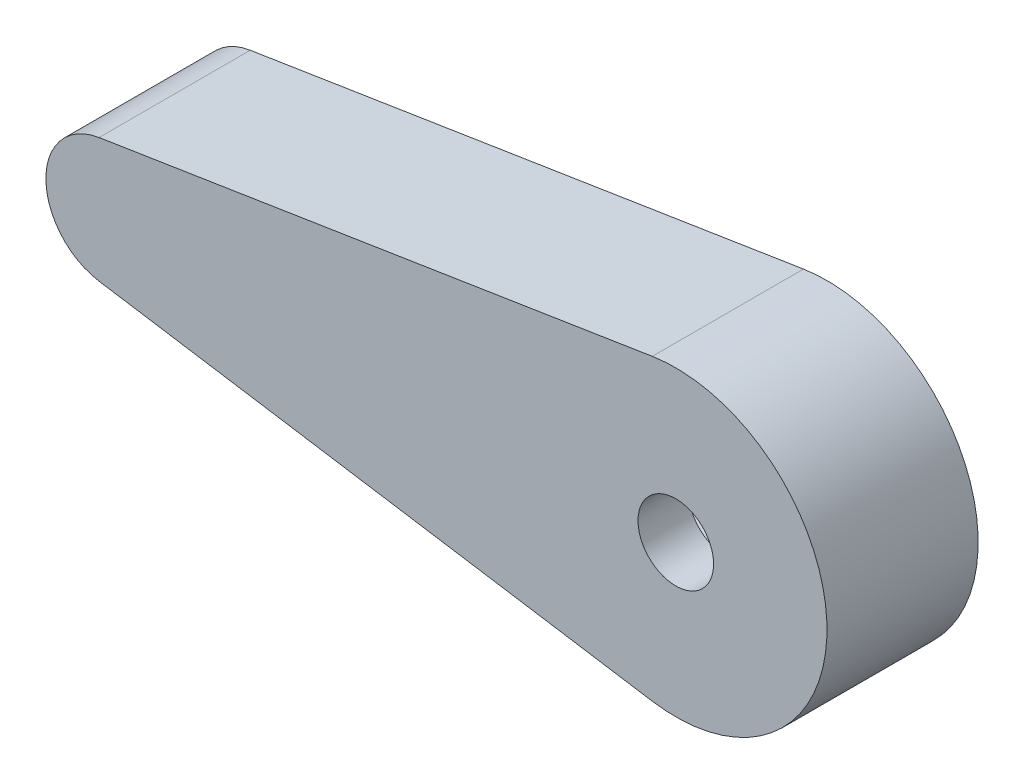
SolidWorks part; units mm, degrees
ref_plane "Top Plane" through (0, 0, 0) normal (0, 0, 1) x (1, 0, 0)
ref_plane "Right Plane" through (0, 0, 0) normal (0, 1, 0) x (1, 0, 0)
ref_plane "Front Plane" through (0, 0, 0) normal (1, 0, 0) x (0, 0, -1)
sketch "Sketch1" plane through (0, 0, 0) normal (0, 0, 1) x (1, 0, 0)
  line L0 (0, 0) -> (-22.5, 0) construction
  line L1 (-22.8889, -2.4696) -> (-0.9333, -5.927)
  line L3 (-22.8889, 2.4696) -> (-0.9333, 5.927)
  arc A0 (-0.9333, -5.927) -> (-0.9333, 5.927) centre (0, 0) ccw
  arc A1 (-22.8889, 2.4696) -> (-22.8889, -2.4696) centre (-22.5, 0) ccw
  point P1 (-25, 0)
  dimension "D1" = 12
  dimension "D2" = 5
  dimension "D3" = 25
extrude "Boss-Extrude1" add sketch "Sketch1" along normal blind 2
sketch "Sketch2" plane through (0, 0, 0) normal (0, 0, -1) x (-1, 0, 0)
  line L0 (14.05, 0) -> (0, 0) construction
  line L1 (14.1755, 2.2966) -> (2.3225, 2.9443)
  line L2 (2.2091, 2.65) -> (14.1591, 1.997) construction
  line L3 (14.1755, -2.2966) -> (2.3225, -2.9443)
  line L4 (14.1591, -1.997) -> (2.2091, -2.65) construction
  line L5 (2.2091, 2.65) -> (14.1591, 1.997) construction
  line L6 (14.1591, -1.997) -> (2.2091, -2.65) construction
  line L9 (22.8889, 2.4696) -> (0.9333, 5.927)
  line L10 (0.9333, -5.927) -> (22.8889, -2.4696)
  line L11 (22.8889, 2.4696) -> (0.9333, 5.927)
  line L12 (0.9333, -5.927) -> (22.8889, -2.4696)
  arc A0 (2.3225, 2.9443) -> (2.3225, -2.9443) centre (0, 0) ccw
  arc A1 (2.2091, 2.65) -> (2.2091, -2.65) centre (0, 0) ccw construction
  arc A2 (14.1755, -2.2966) -> (14.1755, 2.2966) centre (14.05, 0) ccw
  arc A3 (14.1591, -1.997) -> (14.1591, 1.997) centre (14.05, 0) ccw construction
  arc A4 (14.1591, -1.997) -> (14.1591, 1.997) centre (14.05, 0) ccw construction
  arc A7 (22.8889, -2.4696) -> (22.8889, 2.4696) centre (22.5, 0) ccw
  arc A8 (0.9333, 5.927) -> (0.9333, -5.927) centre (0, 0) ccw
  arc A9 (22.8889, -2.4696) -> (22.8889, 2.4696) centre (22.5, 0) ccw
  arc A10 (0.9333, 5.927) -> (0.9333, -5.927) centre (0, 0) ccw
  dimension "D1" = 0.3
  dimension "D2" = 0.3
  dimension "D3" = 0
extrude "Boss-Extrude2" add sketch "Sketch2" along normal blind 4
sketch "Sketch3" plane through (0, 0, 0) normal (0, 0, -1) x (-1, 0, 0)
  circle A0 centre (0, 0) radius 1.5
  dimension "D1" = 3
extrude "Cut-Extrude1" cut sketch "Sketch3" against normal through all
